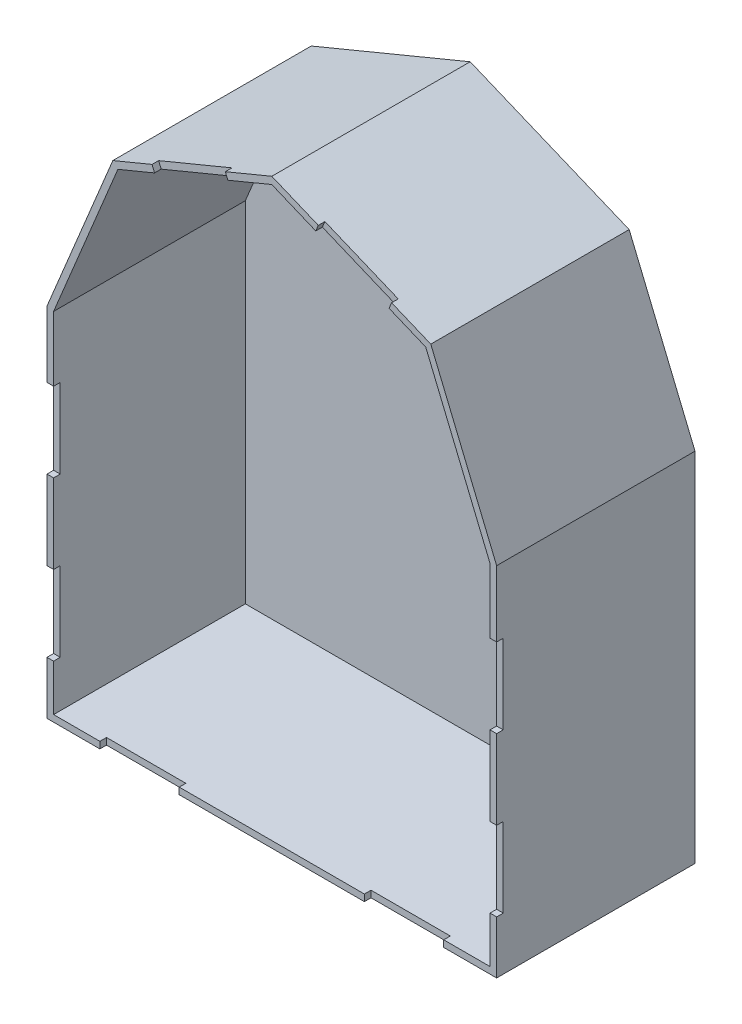
SolidWorks part; units mm, degrees
ref_plane "Front Plane" through (0, 0, 0) normal (0, 0, 1) x (1, 0, 0)
ref_plane "Top Plane" through (0, 0, 0) normal (0, 1, 0) x (1, 0, 0)
ref_plane "Right Plane" through (0, 0, 0) normal (1, 0, 0) x (0, 0, -1)
sketch "Sketch1" plane through (0, 0, 0) normal (0, 0, 1) x (1, 0, 0)
  line L1 (0, 0) -> (170, 0)
  line L2 (0, 0) -> (0, 135)
  line L3 (0, 135) -> (170, 135) construction
  line L4 (170, 0) -> (170, 135)
  line L9 (170, 135) -> (145.1041, 195.1041)
  line L10 (145.1041, 195.1041) -> (85, 220)
  line L11 (85, 220) -> (24.8959, 195.1041)
  line L12 (24.8959, 195.1041) -> (0, 135)
  line L13 (54.948, 62.448) -> (85.4419, 49.8169) [skipped]
  line L14 (115.052, 62.448) -> (145.546, 75.079) [skipped]
  line L15 (157.552, 104.948) -> (170.1831, 135.4419) [skipped]
  line L16 (0, 135) -> (12.631, 104.506) [skipped]
  arc A0 (170, 135) -> (0, 135) centre (85, 135) ccw construction
  circle A1 centre (85, 135) radius 79.6846 construction
  point P7 (85, 220)
  dimension "D3" = 159.3692
  dimension "D1" = 170
  dimension "D2" = 220
extrude "Boss-Extrude1" add sketch "Sketch1" along normal blind 75 contours L4 L9 L10 L11 L12 L2 L1
sketch "Sketch2" plane through (0, 0, 75) normal (0, 0, 1) x (1, 0, 0)
  line L14 (167.5, 134.5027) -> (143.1907, 193.1907)
  line L15 (143.1907, 193.1907) -> (85, 217.294)
  line L16 (85, 217.294) -> (26.8093, 193.1907)
  line L17 (26.8093, 193.1907) -> (2.5, 134.5027)
  line L18 (2.5, 134.5027) -> (2.5, 2.5)
  line L19 (2.5, 2.5) -> (167.5, 2.5)
  line L20 (167.5, 2.5) -> (167.5, 134.5027)
  line L21 (167.5, 134.5027) -> (143.1907, 193.1907)
  line L22 (143.1907, 193.1907) -> (85, 217.294)
  line L23 (85, 217.294) -> (26.8093, 193.1907)
  line L24 (26.8093, 193.1907) -> (2.5, 134.5027)
  line L25 (2.5, 134.5027) -> (2.5, 2.5)
  line L26 (2.5, 2.5) -> (167.5, 2.5)
  line L27 (167.5, 2.5) -> (167.5, 134.5027)
  dimension "D1" = 2.5
extrude "Cut-Extrude1" cut sketch "Sketch2" against normal blind 72.5 contours L22 L23 L24 L25 L26 L27 L21
sketch "Sketch6" plane through (0, 0, 75) normal (0, 0, 1) x (1, 0, 0)
  line L0 (2.5, 2.5) -> (167.5, 2.5) construction
  line L1 (120, 2.5) -> (150, 2.5)
  line L2 (120, 2.5) -> (120, 0)
  line L3 (120, 0) -> (150, 0)
  line L4 (150, 2.5) -> (150, 0)
  line L5 (0, 0) -> (170, 0) construction
  line L6 (167.5, 2.5) -> (167.5, 134.5027) construction
  line L7 (167.5, 20) -> (170, 20)
  line L8 (167.5, 20) -> (167.5, 50)
  line L9 (167.5, 50) -> (170, 50)
  line L10 (170, 20) -> (170, 50)
  line L11 (170, 0) -> (170, 135) construction
  line L12 (101.6161, 210.4114) -> (129.3325, 198.9309)
  line L13 (167.5, 80) -> (170, 80)
  line L14 (167.5, 80) -> (167.5, 110)
  line L15 (167.5, 110) -> (170, 110)
  line L16 (170, 80) -> (170, 110)
  line L17 (143.1907, 193.1907) -> (85, 217.294) construction
  line L18 (129.3325, 198.9309) -> (130.2892, 201.2406)
  line L19 (145.1041, 195.1041) -> (85, 220) construction
  line L20 (130.2892, 201.2406) -> (102.5728, 212.7211)
  line L21 (102.5728, 212.7211) -> (101.6161, 210.4114)
  line L22 (85, 220) -> (85, 0) construction
  line L23 (67.4272, 212.7211) -> (68.3839, 210.4114)
  line L24 (39.7108, 201.2406) -> (67.4272, 212.7211)
  line L25 (40.6675, 198.9309) -> (39.7108, 201.2406)
  line L26 (0, 80) -> (0, 110)
  line L27 (2.5, 110) -> (0, 110)
  line L28 (2.5, 80) -> (2.5, 110)
  line L29 (2.5, 80) -> (0, 80)
  line L30 (68.3839, 210.4114) -> (40.6675, 198.9309)
  line L31 (0, 20) -> (0, 50)
  line L32 (2.5, 50) -> (0, 50)
  line L33 (2.5, 20) -> (2.5, 50)
  line L34 (2.5, 20) -> (0, 20)
  line L35 (20, 2.5) -> (20, 0)
  line L36 (50, 0) -> (20, 0)
  line L37 (50, 2.5) -> (50, 0)
  line L38 (50, 2.5) -> (20, 2.5)
  dimension "D1" = 30
  dimension "D2" = 15
  dimension "D3" = 20
  dimension "D4" = 80
  dimension "D5" = 20
  dimension "D6" = 30
  dimension "D7" = 30
  dimension "D8" = 30
extrude "Cut-Extrude4" cut sketch "Sketch6" against normal blind 2.5
sketch "Sketch8" plane through (0, 2.5, 0) normal (0, 1, 0) x (1, 0, 0)
  line L0 (170, -75) -> (170, 0) construction
  line L1 (170, -75) -> (145.1041, -75) construction
  circle A0 centre (150, -40) radius 5
  dimension "D1" = 10
  dimension "D2" = 20
  dimension "D3" = 35
extrude "Cut-Extrude5" cut sketch "Sketch8" against normal blind 5
